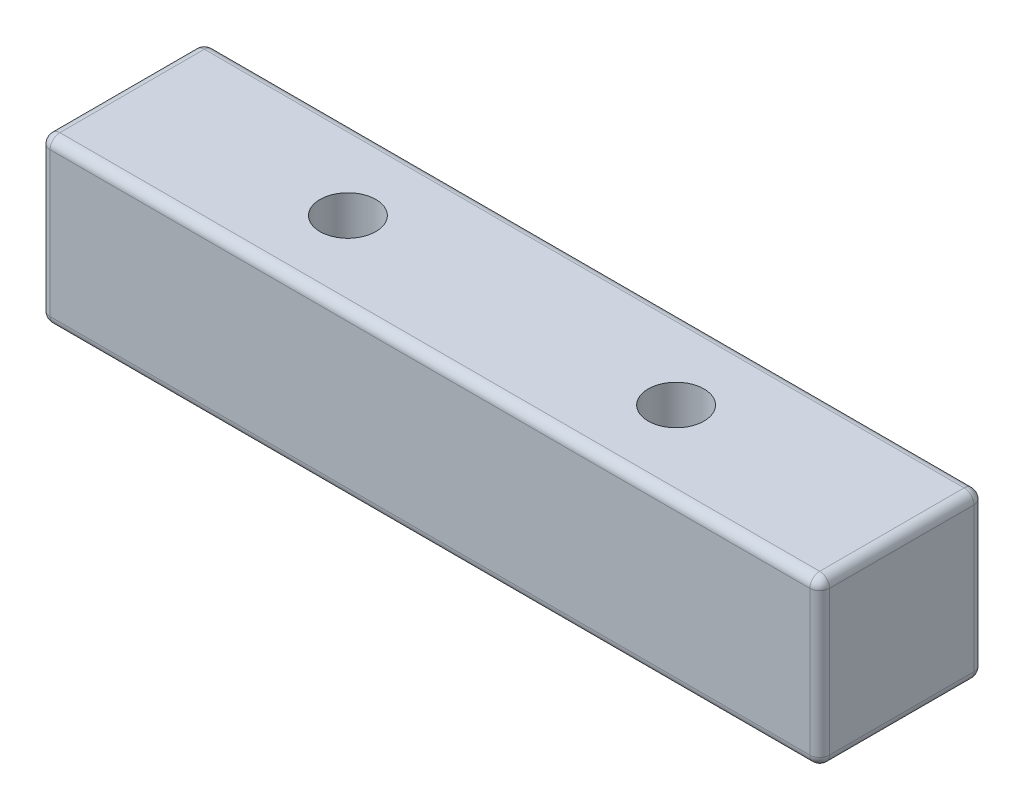
SolidWorks part; units mm, degrees
ref_plane "Front Plane" through (0, 0, 0) normal (0, 0, 1) x (1, 0, 0)
ref_plane "Top Plane" through (0, 0, 0) normal (0, 1, 0) x (1, 0, 0)
ref_plane "Right Plane" through (0, 0, 0) normal (1, 0, 0) x (0, 0, -1)
sketch "Sketch1" plane through (0, 0, 0) normal (0, 1, 0) x (1, 0, 0)
  line L0 (30.1625, 12.7) -> (30.1625, 0) construction
  line L1 (0, 12.7) -> (60.325, 12.7)
  line L2 (0, 12.7) -> (0, 0)
  line L3 (0, 0) -> (60.325, 0)
  line L4 (60.325, 12.7) -> (60.325, 0)
  line L5 (17.4625, 6.35) -> (42.8625, 6.35) construction
  circle A0 centre (17.4625, 6.35) radius 2.159
  circle A1 centre (42.8625, 6.35) radius 2.159
  point P9 (30.1625, 6.35)
  dimension "D3" = 4.318
  dimension "D1" = 12.7
  dimension "D2" = 60.325
  dimension "D4" = 25.4
extrude "Boss-Extrude1" add sketch "Sketch1" along normal blind 12.7
sketch "Sketch5" plane through (0, 0, 0) normal (0, -1, 0) x (1, 0, 0)
  circle A0 centre (42.8625, -6.35) radius 3.556
  circle A1 centre (17.4625, -6.35) radius 3.556
  circle A2 centre (42.8625, -6.35) radius 2.159 construction
  circle A3 centre (17.4625, -6.35) radius 2.159 construction
  dimension "D1" = 7.112
extrude "Cut-Extrude1" cut sketch "Sketch5" against normal blind 3.81
fillet "Fillet1" radius 0.762 14 edges at (30.1625, 12.7, -12.7) (0, 6.35, -12.7) (60.325, 12.7, -6.35) (60.325, 6.35, -12.7) (0, 6.35, 0) (30.1625, 12.7, 0) (60.325, 6.35, 0) (30.1625, 0, 0) (60.325, 0, -6.35) (30.1625, 0, -12.7) (0, 0, -6.35) (17.4625, 0, -9.906) (42.8625, 0, -9.906) (0, 12.7, -6.35)
